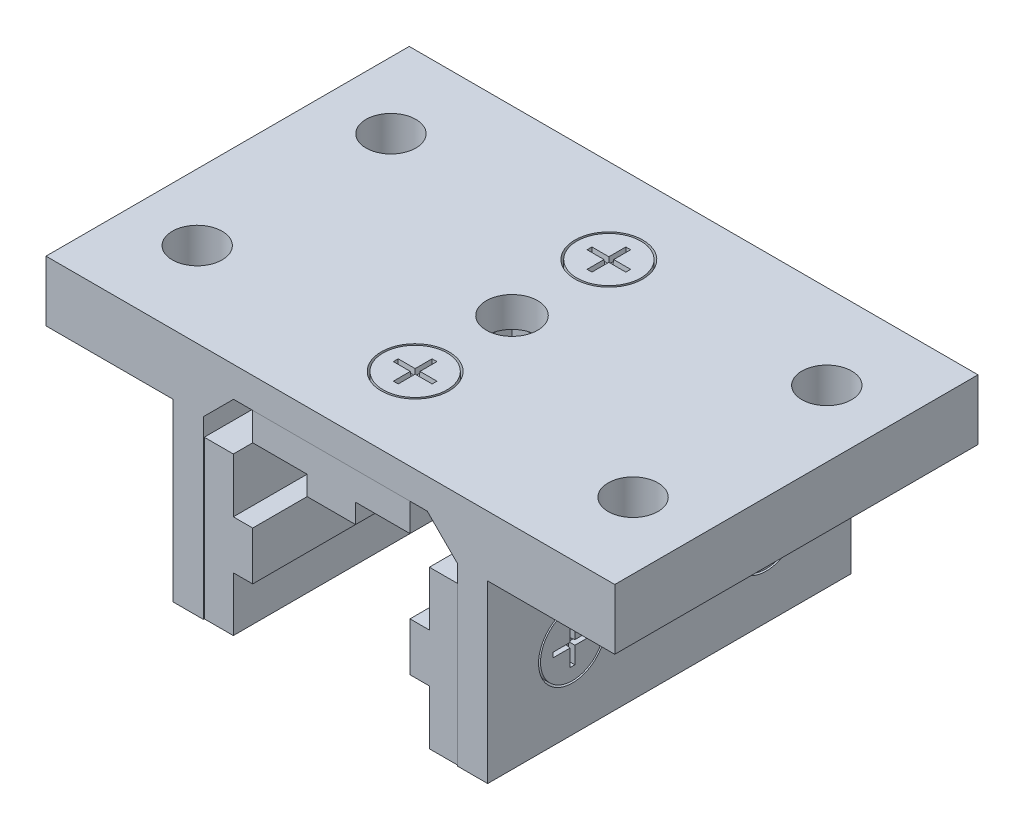
SolidWorks part; units mm, degrees
ref_plane "Front" through (0, 0, 0) normal (0, 0, 1) x (1, 0, 0)
ref_plane "Top" through (0, 0, 0) normal (0, 1, 0) x (1, 0, 0)
ref_plane "Right" through (0, 0, 0) normal (1, 0, 0) x (0, 0, -1)
sketch "Sketch1" plane through (0, 0, 0) normal (0, 0, 1) x (1, 0, 0)
  line L0 (-16.6624, 0) -> (-16.6624, 23.0124)
  line L1 (-20.6248, 30.9372) -> (20.6248, 30.9372)
  line L2 (-20.6248, 30.9372) -> (-20.6248, 0)
  line L3 (-20.6248, 0) -> (-16.6624, 0)
  line L4 (20.6248, 30.9372) -> (20.6248, 0)
  line L5 (-16.6624, 23.0124) -> (-12.7, 26.9748)
  line L6 (-12.7, 26.9748) -> (12.7, 26.9748)
  line L7 (12.7, 26.9748) -> (16.6624, 23.0124)
  line L8 (16.6624, 23.0124) -> (16.6624, 0)
  line L9 (16.6624, 0) -> (20.6248, 0)
  line L11 (-16.6624, 0) -> (16.6624, 0) construction
  dimension "D2" = 45
extrude "Boss-Extrude1" add sketch "Sketch1" along normal mid plane 47.625
sketch "Sketch2" plane through (0, 0, 0) normal (0, 0, 1) x (1, 0, 0)
  line L0 (-12.8524, 13.4874) -> (-12.8524, 20.6248)
  line L1 (-16.6624, 0) -> (-12.8524, 0)
  line L2 (-16.6624, 0) -> (-16.6624, 20.6248)
  line L3 (-16.6624, 20.6248) -> (-12.8524, 20.6248)
  line L4 (-12.8524, 0) -> (-12.8524, 7.1374)
  line L5 (-12.8524, 13.4874) -> (-10.3124, 13.4874)
  line L7 (-12.8524, 7.1374) -> (-10.3124, 7.1374)
  line L8 (-10.3124, 13.4874) -> (-10.3124, 7.1374)
  line L12 (-12.7, 26.9748) -> (12.7, 26.9748) construction
  line L13 (-10.3124, 26.9748) -> (10.3124, 26.9748)
  line L14 (-10.3124, 26.9748) -> (-10.3124, 23.1648)
  line L15 (-10.3124, 23.1648) -> (-3.175, 23.1648)
  line L16 (10.3124, 26.9748) -> (10.3124, 23.1648)
  line L17 (3.175, 23.1648) -> (10.3124, 23.1648)
  line L19 (-3.175, 23.1648) -> (-3.175, 20.6248)
  line L20 (-3.175, 20.6248) -> (3.175, 20.6248)
  line L21 (3.175, 23.1648) -> (3.175, 20.6248)
  point P14 (-10.3124, 10.3124)
  point P28 (0, 26.9748)
  dimension "Pad Wd" = 20.6248
  dimension "Pad Thick 1" = 6.35
  dimension "Pad Thick 2" = 3.81
  dimension "Pad Nose" = 6.35
extrude "Boss-Extrude2" add sketch "Sketch2" along normal mid plane 47.371 separate body
sketch "Sketch11" plane through (-10.3124, 0, 0) normal (1, 0, 0) x (0, 0, -1)
  line L0 (-23.6855, 13.4874) -> (23.6855, 13.4874) construction
  line L1 (-3.175, 13.4874) -> (3.175, 13.4874)
  line L2 (-3.175, 13.4874) -> (-3.175, 7.1374)
  line L3 (-3.175, 7.1374) -> (3.175, 7.1374)
  line L4 (3.175, 13.4874) -> (3.175, 7.1374)
  line L5 (-23.6855, 7.1374) -> (23.6855, 7.1374) construction
  point P8 (0, 13.4874)
extrude "Cut-Extrude5" cut sketch "Sketch11" against normal through all
sketch "Sketch12" plane through (0, 20.6248, 0) normal (0, -1, 0) x (1, 0, 0)
  line L0 (-3.175, 23.6855) -> (-3.175, -23.6855) construction
  line L1 (-3.175, 3.175) -> (3.175, 3.175)
  line L2 (-3.175, 3.175) -> (-3.175, -3.175)
  line L3 (-3.175, -3.175) -> (3.175, -3.175)
  line L4 (3.175, 3.175) -> (3.175, -3.175)
  line L5 (3.175, 23.6855) -> (3.175, -23.6855) construction
  point P8 (-3.175, 0)
extrude "Cut-Extrude6" cut sketch "Sketch12" against normal through all
mirror "Mirror1" about plane through (0, 0, 0) normal (1, 0, 0) of bodies 126 109
sketch "Sketch3" plane through (0, 30.9372, 0) normal (0, 1, 0) x (1, 0, 0)
  line L0 (0, -12.7) -> (0, 12.7) construction
  circle A0 centre (0, -12.7) radius 4.445
  circle A1 centre (0, -12.7) radius 4.191
extrude "Cut-Extrude1" cut sketch "Sketch3" against normal blind 1.9812
sketch "Sketch5" plane through (0, 30.9372, 0) normal (0, 1, 0) x (1, 0, 0)
  line L0 (0.3175, -12.3825) -> (2.54, -12.3825)
  line L1 (-0.3175, -10.16) -> (0.3175, -10.16)
  line L2 (-0.3175, -10.16) -> (-0.3175, -12.3825)
  line L3 (-0.3175, -15.24) -> (0.3175, -15.24)
  line L4 (0.3175, -10.16) -> (0.3175, -12.3825)
  line L5 (-2.54, -12.3825) -> (-0.3175, -12.3825)
  line L6 (-2.54, -12.3825) -> (-2.54, -13.0175)
  line L7 (-2.54, -13.0175) -> (-0.3175, -13.0175)
  line L8 (2.54, -12.3825) -> (2.54, -13.0175)
  line L9 (-0.3175, -13.0175) -> (-0.3175, -15.24)
  line L10 (0.3175, -13.0175) -> (0.3175, -15.24)
  line L11 (0.3175, -13.0175) -> (2.54, -13.0175)
  line L12 (-0.3175, -12.3825) -> (0.3175, -13.0175) construction
  dimension "D1" = 0.635
  dimension "D2" = 5.08
extrude "Cut-Extrude2" cut sketch "Sketch5" against normal blind 0.762 draft 5
sketch "Sketch13" plane through (20.6248, 0, 0) normal (1, 0, 0) x (0, 0, -1)
  circle A0 centre (-12.7, 10.3124) radius 4.445
  dimension "D1" = 8.89
extrude "Cut-Extrude-Thin1" cut sketch "Sketch13" against normal blind 1.9812 thin thin type one direction reverse wall 0.254
sketch "Sketch14" plane through (20.6248, 0, 0) normal (1, 0, 0) x (0, 0, -1)
  line L0 (-13.0175, 9.9949) -> (-13.0175, 7.7724)
  line L1 (-13.0175, 12.8524) -> (-12.3825, 12.8524)
  line L2 (-13.0175, 12.8524) -> (-13.0175, 10.6299)
  line L3 (-13.0175, 7.7724) -> (-12.3825, 7.7724)
  line L4 (-12.3825, 12.8524) -> (-12.3825, 10.6299)
  line L5 (-15.24, 10.6299) -> (-13.0175, 10.6299)
  line L6 (-15.24, 10.6299) -> (-15.24, 9.9949)
  line L7 (-15.24, 9.9949) -> (-13.0175, 9.9949)
  line L8 (-10.16, 10.6299) -> (-10.16, 9.9949)
  line L9 (-12.3825, 10.6299) -> (-10.16, 10.6299)
  line L10 (-12.3825, 9.9949) -> (-12.3825, 7.7724)
  line L11 (-12.3825, 9.9949) -> (-10.16, 9.9949)
  line L12 (-13.0175, 10.6299) -> (-12.3825, 9.9949) construction
  dimension "D1" = 0.635
  dimension "D2" = 5.08
extrude "Cut-Extrude7" cut sketch "Sketch14" against normal blind 0.762 draft 5
mirror "Mirror4" about plane through (0, 0, 0) normal (1, 0, 0) of "Cut-Extrude7", "Cut-Extrude-Thin1"
mirror "Mirror3" about plane through (0, 0, 0) normal (0, 0, 1) of "Mirror4", "Cut-Extrude-Thin1", "Cut-Extrude7", "Cut-Extrude1", "Cut-Extrude2"
sketch "Sketch9" plane through (0, 30.9372, 0) normal (0, 1, 0) x (1, 0, 0)
  circle A0 centre (0, 0) radius 3.3655
  dimension "Top Hole Dia" = 6.731
extrude "Cut-Extrude4" cut sketch "Sketch9" against normal through all
sketch "Sketch15" plane through (0, 0, 0) normal (1, 0, 0) x (0, 0, -1)
  circle A0 centre (0, 10.3124) radius 3.3655
  dimension "Side Wall Hole Dia" = 6.731
extrude "Cut-Extrude8" cut sketch "Sketch15" against normal through all and the other way through all
sketch "Sketch16" plane through (0, 0, 0) normal (0, 0, 1) x (1, 0, 0)
  line L1 (-37.2872, 30.9372) -> (-18.6436, 30.9372)
  line L2 (-37.2872, 30.9372) -> (-37.2872, 23.0124)
  line L3 (-37.2872, 23.0124) -> (-18.6436, 23.0124)
  line L4 (-18.6436, 30.9372) -> (-18.6436, 23.0124)
  line L5 (20.6248, 30.9372) -> (-20.6248, 30.9372) construction
  line L6 (18.6436, 30.9372) -> (37.2872, 30.9372)
  line L7 (18.6436, 30.9372) -> (18.6436, 23.0124)
  line L8 (18.6436, 23.0124) -> (37.2872, 23.0124)
  line L9 (37.2872, 30.9372) -> (37.2872, 23.0124)
  line L10 (-20.6248, 0) -> (-16.6624, 0) construction
  line L11 (16.6624, 0) -> (20.6248, 0) construction
  point P4 (-18.6436, 0)
  point P13 (18.6436, 0)
  dimension "Oall Wd" = 74.5744
  dimension "Top Flange Thickness" = 7.9248
extrude "Top Flange" add sketch "Sketch16" along normal up to surface and the other way up to surface
sketch "Sketch17" plane through (0, 30.9372, 0) normal (0, 1, 0) x (1, 0, 0)
  line L0 (-28.575, 12.7) -> (28.575, -12.7) construction
  line L1 (-28.575, 12.7) -> (28.575, 12.7) construction
  line L2 (-28.575, 12.7) -> (-28.575, -12.7) construction
  line L3 (-28.575, -12.7) -> (28.575, -12.7) construction
  line L4 (28.575, 12.7) -> (28.575, -12.7) construction
  line L5 (-18.6436, 12.7) -> (-20.6248, 12.7) construction
  circle A0 centre (28.575, 12.7) radius 3.2639
  circle A1 centre (28.575, -12.7) radius 3.2639
  circle A2 centre (-28.575, 12.7) radius 3.2639
  circle A3 centre (-28.575, -12.7) radius 3.2639
  dimension "Top Flange Hole Dia" = 6.5278
  dimension "Top Flange Hole Spacing" = 57.15
extrude "Top Flange Hole" cut sketch "Sketch17" against normal through all
mirror "Mirror7" [suppressed]
mirror "Mirror6" [suppressed]
other "Delete Hole Short" [suppressed]
other "Delete Hole Long" [suppressed]
pattern_linear "LPattern1" [suppressed] count 2 count 2 spacing 19.05
sketch "Sketch19" [suppressed] plane through (0, 0, 0) normal (0, 0, 1) x (1, 0, 0)
  line L0 (-23.622, 47.625) -> (-14.478, 47.625) construction
  line L1 (-88.9, 47.625) -> (-23.622, 47.625)
  line L2 (-88.9, 47.625) -> (-88.9, 0)
  line L3 (-88.9, 0) -> (-23.622, 0)
  line L4 (-23.622, 47.625) -> (-23.622, 0)
  line L5 (14.478, 47.625) -> (-14.478, 47.625)
  line L6 (14.478, 47.625) -> (14.478, 0)
  line L7 (14.478, 0) -> (-14.478, 0)
  line L8 (-14.478, 47.625) -> (-14.478, 0)
  line L9 (-69.85, 0) -> (-63.5, 0) construction
  line L11 (14.478, 47.625) -> (23.622, 47.625) construction
  line L12 (23.622, 47.625) -> (88.9, 47.625)
  line L13 (23.622, 47.625) -> (23.622, 0)
  line L14 (23.622, 0) -> (88.9, 0)
  line L15 (88.9, 47.625) -> (88.9, 0)
  line L17 (-22.987, 31.75) -> (-15.113, 31.75) construction
  line L18 (15.113, 31.75) -> (22.987, 31.75) construction
  point P8 (-19.05, 47.625)
  point P9 (-19.05, 31.75)
  point P12 (19.05, 31.75)
  point P19 (19.05, 47.625)
  dimension "D1" = 9.144
extrude "Cut-Extrude12" [suppressed] cut sketch "Sketch19" against normal through all and the other way through all flip side to cut
sketch "Sketch20" [suppressed] plane through (0, 0, 0) normal (0, 0, 1) x (1, 0, 0)
  line L4 (14.478, 47.625) -> (-14.478, 47.625)
  line L5 (-14.478, 47.625) -> (-14.478, 0)
  line L6 (-14.478, 0) -> (14.478, 0)
  line L7 (14.478, 0) -> (14.478, 47.625)
  line L8 (88.9, 47.625) -> (-14.478, 47.625)
  line L9 (-14.478, 47.625) -> (-14.478, 0)
  line L10 (-14.478, 0) -> (88.9, 0)
  line L12 (-23.622, 47.625) -> (-88.9, 47.625)
  line L13 (-23.622, 0) -> (-23.622, 47.625)
  line L14 (-88.9, 0) -> (-23.622, 0)
  line L15 (-88.9, 47.625) -> (-88.9, 0)
  line L16 (-23.622, 47.625) -> (-88.9, 47.625)
  line L17 (-23.622, 0) -> (-23.622, 47.625)
  line L18 (-88.9, 0) -> (-23.622, 0)
  line L19 (-88.9, 47.625) -> (-88.9, 0)
  line L20 (88.9, 47.625) -> (23.622, 47.625)
  line L21 (23.622, 47.625) -> (23.622, 0)
  line L22 (23.622, 0) -> (88.9, 0)
  line L23 (88.9, 0) -> (88.9, 47.625)
  line L27 (88.9, 0) -> (88.9, 47.625)
  dimension "D1" = 0
  dimension "D2" = 0
  dimension "D3" = 0
extrude "Cut-Extrude14" [suppressed] cut sketch "Sketch20" against normal through all and the other way through all
sketch "Sketch21" [suppressed] plane through (0, 0, 0) normal (0, 0, 1) x (1, 0, 0)
  line L4 (14.478, 47.625) -> (-14.478, 47.625)
  line L5 (-14.478, 47.625) -> (-14.478, 0)
  line L6 (-14.478, 0) -> (14.478, 0)
  line L7 (14.478, 0) -> (14.478, 47.625)
  line L8 (14.478, 47.625) -> (-88.9, 47.625)
  line L10 (-88.9, 0) -> (14.478, 0)
  line L11 (14.478, 0) -> (14.478, 47.625)
  line L12 (-23.622, 47.625) -> (-88.9, 47.625)
  line L13 (-23.622, 0) -> (-23.622, 47.625)
  line L14 (-88.9, 0) -> (-23.622, 0)
  line L15 (-88.9, 47.625) -> (-88.9, 0)
  line L19 (-88.9, 47.625) -> (-88.9, 0)
  line L20 (88.9, 47.625) -> (23.622, 47.625)
  line L21 (23.622, 47.625) -> (23.622, 0)
  line L22 (23.622, 0) -> (88.9, 0)
  line L23 (88.9, 0) -> (88.9, 47.625)
  line L24 (88.9, 47.625) -> (23.622, 47.625)
  line L25 (23.622, 47.625) -> (23.622, 0)
  line L26 (23.622, 0) -> (88.9, 0)
  line L27 (88.9, 0) -> (88.9, 47.625)
  dimension "D1" = 0
  dimension "D2" = 0
  dimension "D3" = 0
extrude "Cut-Extrude15" [suppressed] cut sketch "Sketch21" against normal through all and the other way through all
sketch "Sketch22" [suppressed] plane through (0, 0, 38.1) normal (0, 0, 1) x (1, 0, 0)
  line L4 (-14.478, 41.275) -> (14.478, 41.275)
  line L5 (14.478, 41.275) -> (14.478, 47.625)
  line L6 (14.478, 47.625) -> (-14.478, 47.625)
  line L7 (14.478, 41.275) -> (14.478, 47.625)
  line L8 (-14.478, 41.275) -> (14.478, 41.275)
  line L9 (-14.478, 47.625) -> (-14.478, 41.275)
  line L10 (14.478, 47.625) -> (-14.478, 47.625)
  line L11 (-14.478, 47.625) -> (-14.478, 41.275)
  dimension "D1" = 0
extrude "Boss-Extrude4" [suppressed] add sketch "Sketch22" against normal through all
combine bodies "Combine1" [suppressed] operation type add bodies to combine 160 166 170 159 167
delete or keep bodies "Body-Delete1" [suppressed] type delete bodies bodies 128 138
pattern_linear "LPattern2" [suppressed] count 2 count 2 spacing 19.05
sketch "Sketch23" [suppressed] plane through (0, 0, 0) normal (0, 0, 1) x (1, 0, 0)
  line L0 (-15.875, 20.6248) -> (-9.525, 20.6248) construction
  line L1 (-82.55, 47.625) -> (-17.272, 47.625)
  line L2 (-82.55, 47.625) -> (-82.55, 0)
  line L3 (-82.55, 0) -> (-17.272, 0)
  line L4 (-17.272, 47.625) -> (-17.272, 0)
  line L5 (82.55, 47.625) -> (17.272, 47.625)
  line L6 (82.55, 47.625) -> (82.55, 0)
  line L7 (82.55, 0) -> (17.272, 0)
  line L8 (17.272, 47.625) -> (17.272, 0)
  line L9 (-17.272, 47.625) -> (-8.128, 47.625) construction
  line L10 (-8.128, 47.625) -> (8.128, 47.625)
  line L11 (-8.128, 47.625) -> (-8.128, 0)
  line L12 (-8.128, 0) -> (8.128, 0)
  line L13 (8.128, 47.625) -> (8.128, 0)
  line L14 (8.128, 47.625) -> (17.272, 47.625) construction
  line L15 (-63.5, 0) -> (-57.15, 0) construction
  line L16 (9.525, 20.6248) -> (15.875, 20.6248) construction
  point P10 (-12.7, 47.625)
  point P11 (12.7, 47.625)
  point P17 (-12.7, 20.6248)
  point P18 (12.7, 20.6248)
  dimension "D1" = 9.144
extrude "Cut-Extrude16" [suppressed] cut sketch "Sketch23" against normal through all and the other way through all flip side to cut
sketch "Sketch24" [suppressed] plane through (0, 0, 0) normal (0, 0, 1) x (1, 0, 0)
  line L4 (8.128, 47.625) -> (-8.128, 47.625)
  line L5 (8.128, 0) -> (8.128, 47.625)
  line L6 (-8.128, 0) -> (8.128, 0)
  line L7 (-8.128, 47.625) -> (-8.128, 0)
  line L8 (82.55, 47.625) -> (-8.128, 47.625)
  line L10 (-8.128, 0) -> (82.55, 0)
  line L11 (-8.128, 47.625) -> (-8.128, 0)
  line L12 (82.55, 47.625) -> (17.272, 47.625)
  line L13 (17.272, 47.625) -> (17.272, 0)
  line L14 (17.272, 0) -> (82.55, 0)
  line L15 (82.55, 0) -> (82.55, 47.625)
  line L19 (82.55, 0) -> (82.55, 47.625)
  line L20 (-17.272, 47.625) -> (-82.55, 47.625)
  line L21 (-17.272, 0) -> (-17.272, 47.625)
  line L22 (-82.55, 0) -> (-17.272, 0)
  line L23 (-82.55, 47.625) -> (-82.55, 0)
  line L24 (-17.272, 47.625) -> (-82.55, 47.625)
  line L25 (-17.272, 0) -> (-17.272, 47.625)
  line L26 (-82.55, 0) -> (-17.272, 0)
  line L27 (-82.55, 47.625) -> (-82.55, 0)
  dimension "D1" = 0
  dimension "D2" = 0
  dimension "D3" = 0
extrude "Cut-Extrude17" [suppressed] cut sketch "Sketch24" against normal through all and the other way through all
sketch "Sketch25" [suppressed] plane through (0, 0, 0) normal (0, 0, 1) x (1, 0, 0)
  line L4 (8.128, 47.625) -> (-8.128, 47.625)
  line L5 (8.128, 0) -> (8.128, 47.625)
  line L6 (-8.128, 0) -> (8.128, 0)
  line L7 (-8.128, 47.625) -> (-8.128, 0)
  line L8 (8.128, 47.625) -> (-82.55, 47.625)
  line L9 (8.128, 0) -> (8.128, 47.625)
  line L10 (-82.55, 0) -> (8.128, 0)
  line L12 (82.55, 47.625) -> (17.272, 47.625)
  line L13 (17.272, 47.625) -> (17.272, 0)
  line L14 (17.272, 0) -> (82.55, 0)
  line L15 (82.55, 0) -> (82.55, 47.625)
  line L16 (82.55, 47.625) -> (17.272, 47.625)
  line L17 (17.272, 47.625) -> (17.272, 0)
  line L18 (17.272, 0) -> (82.55, 0)
  line L19 (82.55, 0) -> (82.55, 47.625)
  line L20 (-17.272, 47.625) -> (-82.55, 47.625)
  line L21 (-17.272, 0) -> (-17.272, 47.625)
  line L22 (-82.55, 0) -> (-17.272, 0)
  line L23 (-82.55, 47.625) -> (-82.55, 0)
  line L27 (-82.55, 47.625) -> (-82.55, 0)
  dimension "D1" = 0
  dimension "D2" = 0
  dimension "D3" = 0
extrude "Cut-Extrude18" [suppressed] cut sketch "Sketch25" against normal through all and the other way through all
sketch "Sketch26" [suppressed] plane through (0, 0, 38.1) normal (0, 0, 1) x (1, 0, 0)
  line L4 (8.128, 47.625) -> (-8.128, 47.625)
  line L5 (-8.128, 47.625) -> (-8.128, 41.275)
  line L6 (-8.128, 41.275) -> (8.128, 41.275)
  line L7 (8.128, 41.275) -> (8.128, 47.625)
  line L8 (8.128, 47.625) -> (-8.128, 47.625)
  line L9 (-8.128, 47.625) -> (-8.128, 41.275)
  line L10 (-8.128, 41.275) -> (8.128, 41.275)
  line L11 (8.128, 41.275) -> (8.128, 47.625)
  dimension "D1" = 0
extrude "Boss-Extrude5" [suppressed] add sketch "Sketch26" against normal through all
combine bodies "Combine2" [suppressed] operation type add bodies to combine 181 179 184 180 182
delete or keep bodies "Body-Delete4" [suppressed] type delete bodies bodies 128
sketch "Sketch27" plane through (0, 30.9372, 0) normal (0, 1, 0) x (1, 0, 0)
  line L0 (-31.8389, 12.7) -> (31.8389, 12.7) construction
  circle A0 centre (-28.575, 12.7) radius 3.2639 construction
  circle A1 centre (28.575, 12.7) radius 3.2639 construction
equation "\"D1@Cut-Extrude1\" = \"Top Thick@Sketch1\" * .5"
equation "\"D1@Sketch13\" = \"Screw Head Dia@Sketch3\""
equation "\"D1@Cut-Extrude-Thin1\" = \"Leg Thick@Sketch1\" * .5"
equation "\"D5@Cut-Extrude-Thin1\" = \"D1@Sketch3\""
equation "\"D1@Cut-Extrude7\" = \"D1@Cut-Extrude2\""
equation "\"D1@Sketch14\" = \"D1@Sketch5\""
equation "\"D2@Sketch14\" = \"D2@Sketch5\""
equation "\"D3@Cut-Extrude7\" = \"D3@Cut-Extrude2\""
equation "\"D4@LPattern1\" = \"Double Wd Offset@LPattern1\""
equation "\"D4@LPattern2\" = \"Double Wd Offset@LPattern2\""
